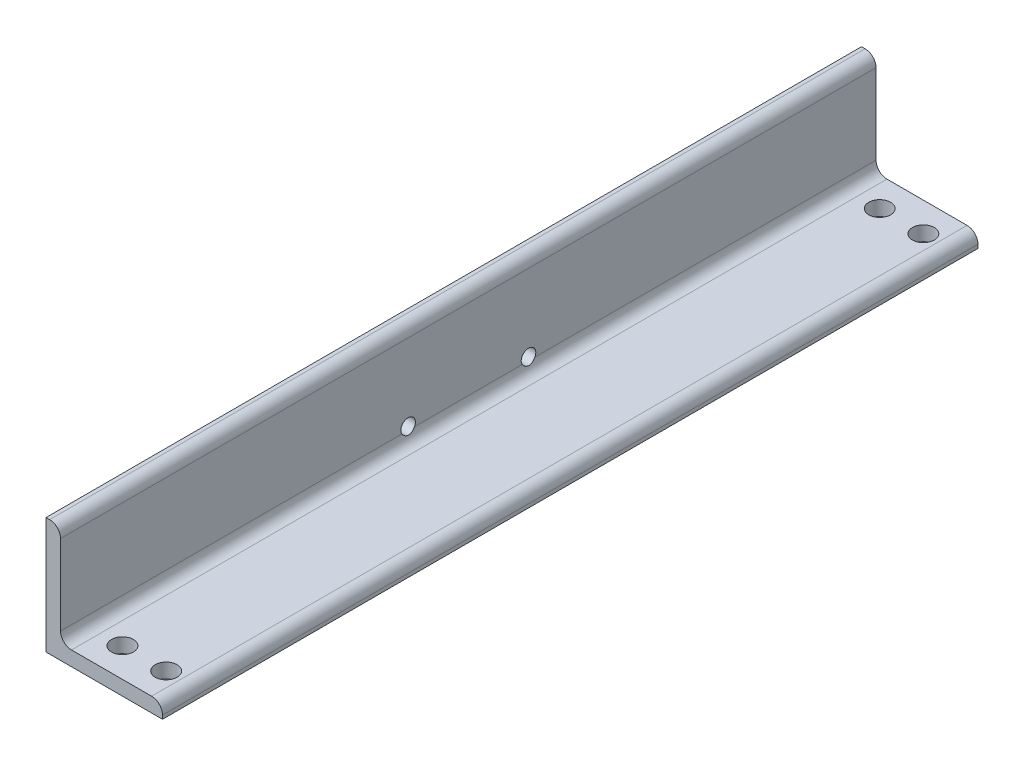
SolidWorks part; units mm, degrees
ref_plane "Front Plane" through (0, 0, 0) normal (0, 0, 1) x (1, 0, 0)
ref_plane "Top Plane" through (0, 0, 0) normal (0, 1, 0) x (1, 0, 0)
ref_plane "Right Plane" through (0, 0, 0) normal (1, 0, 0) x (0, 0, -1)
sketch "Sketch1" plane through (0, 0, 0) normal (0, 0, 1) x (1, 0, 0)
  line L0 (0, 0) -> (0, 101.6)
  line L1 (0, 101.6) -> (3.1801, 101.6)
  line L2 (12.7, 92.0801) -> (12.7, 22.225)
  line L3 (22.225, 12.7) -> (92.0801, 12.7)
  line L4 (101.6, 3.1801) -> (101.6, 0)
  line L5 (101.6, 0) -> (0, 0)
  arc A0 (101.6, 3.1801) -> (92.0801, 12.7) centre (92.0801, 3.1801) ccw
  arc A1 (3.1801, 101.6) -> (12.7, 92.0801) centre (3.1801, 92.0801) cw
  arc A2 (22.225, 12.7) -> (12.7, 22.225) centre (22.225, 22.225) cw
  circle A3 centre (0, 0) radius 9.525 construction
  dimension "D2" = 3.1801
  dimension "Radius_1" = 9.525
  dimension "Radius_2" = 9.525
  dimension "D1" = 12.7
  dimension "V_leg" = 101.6
  dimension "H_leg" = 101.6
  dimension "Thickness" = 12.7
  dimension "Flat_wid" = 3.1801
extrude "Boss-Extrude1" add sketch "Sketch1" along normal mid plane 711.2
sketch "Sketch3" plane through (25.4, 12.7, 0) normal (0, 1, 0) x (0, 0, -1)
  line L0 (355.6, -34.925) -> (355.6, 3.175) construction
  line L1 (-355.6, 25.4) -> (355.6, 25.4) construction
  line L2 (355.6, -34.925) -> (-165.1, -34.925) construction
  line L5 (0, 12.7) -> (0, 20.3926) construction
  line L6 (-355.6, 12.7) -> (355.6, 12.7) construction
  circle A0 centre (330.2, -15.875) radius 9.525
  circle A1 centre (-330.2, -15.875) radius 9.525
  circle A2 centre (-330.2, -53.975) radius 9.525
  circle A3 centre (330.2, -53.975) radius 9.525
  dimension "D1" = 19.05
  dimension "D3" = 19.05
  dimension "D2" = 330.2
  dimension "D4" = 41.275
extrude "Cut-Extrude1" cut sketch "Sketch3" against normal up to next
sketch "Sketch4" plane through (0, 0, 0) normal (-1, 0, 0) x (0, 0, 1)
  line L0 (-52.4891, 25.4) -> (52.4891, 25.4) construction
  line L1 (0, 25.4) -> (0, 0) construction
  line L2 (355.6, 0) -> (-355.6, 0) construction
  circle A0 centre (-52.4891, 25.4) radius 6.35
  circle A1 centre (52.4891, 25.4) radius 6.35
  dimension "D1" = 12.7
  dimension "D2" = 104.9782
  dimension "D3" = 25.4
extrude "Cut-Extrude2" cut sketch "Sketch4" against normal up to next
